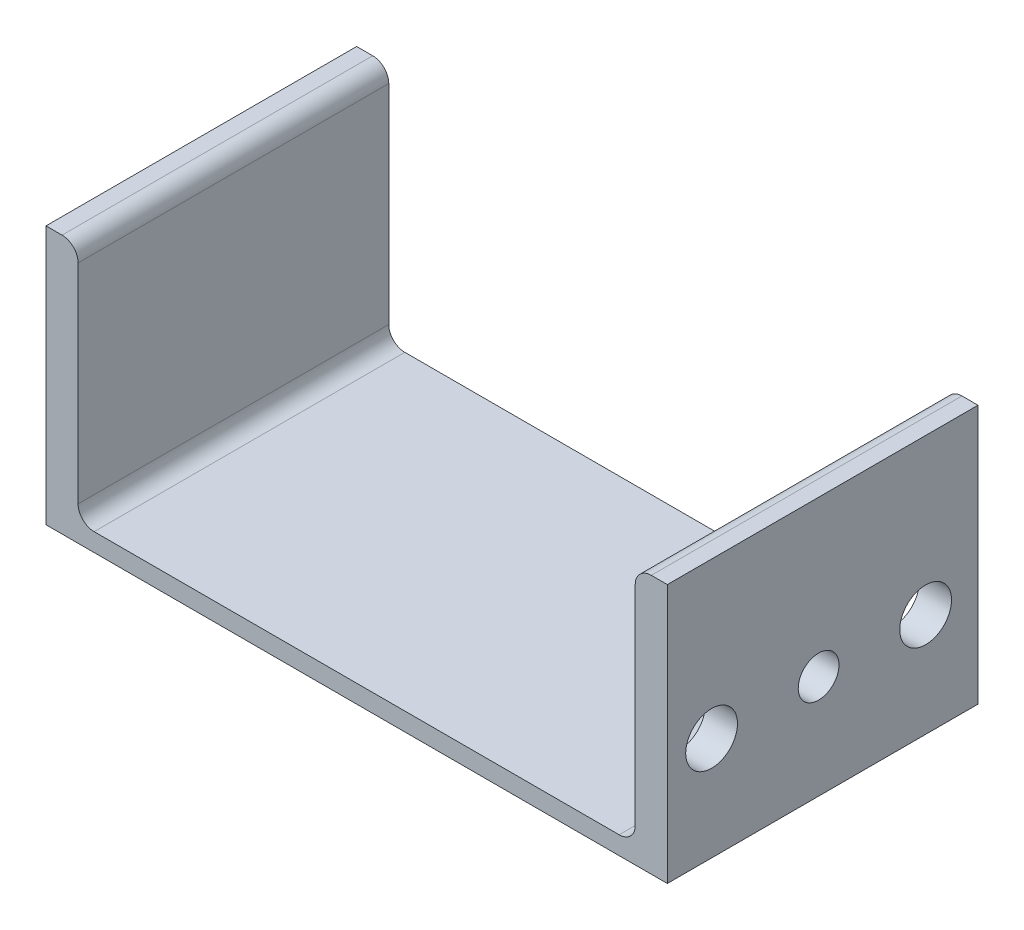
SolidWorks part; units mm, degrees
ref_plane "Front" through (0, 0, 0) normal (0, 0, 1) x (1, 0, 0)
ref_plane "Top" through (0, 0, 0) normal (0, 1, 0) x (1, 0, 0)
ref_plane "Right" through (0, 0, 0) normal (1, 0, 0) x (0, 0, -1)
sketch "Sketch1" plane through (0, 0, 0) normal (0, 0, 1) x (1, 0, 0)
  line L0 (-136.652, 127) -> (-152.4, 127)
  line L1 (-152.4, 127) -> (-152.4, 0)
  line L2 (-152.4, 0) -> (152.4, 0)
  line L3 (152.4, 0) -> (152.4, 127)
  line L4 (152.4, 127) -> (136.652, 127)
  line L5 (136.652, 127) -> (136.652, 8.89)
  line L6 (136.652, 8.89) -> (-136.652, 8.89)
  line L7 (-136.652, 8.89) -> (-136.652, 127)
  dimension "Leg THickness" = 15.748
  dimension "BaseThickness" = 8.89
  dimension "LegLength" = 127
  dimension "BaseWidth" = 304.8
extrude "Boss-Extrude1" add sketch "Sketch1" along normal mid plane 152.4
fillet "Fillet1" radius 7.874 4 edges at (136.652, 127, 0) (-136.652, 127, 0) (-136.652, 8.89, 0) (136.652, 8.89, 0)
sketch "Sketch3" plane through (152.4, 0, 0) normal (1, 0, 0) x (0, 0, -1)
  line L0 (-1.9931, 50.8) -> (-1.9931, 80.2035) construction
  circle A0 centre (50.5069, 50.8) radius 12.7
  circle A1 centre (-54.4931, 50.8) radius 12.7
  circle A2 centre (-1.9931, 50.8) radius 10
  point P7 (-1.9931, 41.4464)
  point P8 (0, 0)
  dimension "D1" = 25.4
  dimension "D3" = 20
  dimension "D2" = 52.5
  dimension "D4" = 50.8
extrude "Cut-Extrude1" cut sketch "Sketch3" against normal up to surface (15.748 mm away) up to face at (136.652, 67.945, 0)
equation "\"D1@Fillet1\" = \"Leg THickness@Sketch1\"/2"
